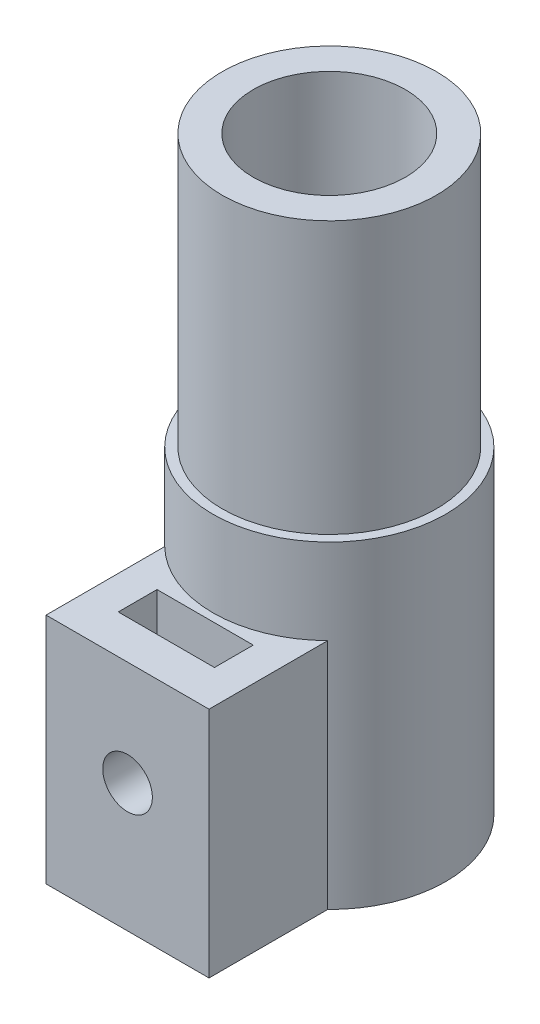
SolidWorks part; units mm, degrees
ref_plane "Front Plane" through (0, 0, 0) normal (0, 0, 1) x (1, 0, 0)
ref_plane "Top Plane" through (0, 0, 0) normal (0, 1, 0) x (1, 0, 0)
ref_plane "Right Plane" through (0, 0, 0) normal (1, 0, 0) x (0, 0, -1)
sketch "Sketch1" plane through (0, 0, 0) normal (0, 1, 0) x (1, 0, 0)
  circle A0 centre (0, 0) radius 6.9
  circle A1 centre (0, 0) radius 4.9
  dimension "D1" = 13.8
  dimension "D2" = 2
extrude "Boss-Extrude1" add sketch "Sketch1" against normal blind 38 contours A0
ref_plane "Plane1" through (0, -17.5, 0) normal (0, -1, 0) x (-1, 0, 0)
sketch "Sketch2" plane through (0, -17.5, 0) normal (0, -1, 0) x (-1, 0, 0)
  circle A0 centre (0, 0) radius 7.5
  circle A1 centre (0, 0) radius 6.9 construction
  circle A2 centre (0, 0) radius 6.9
  dimension "D1" = 15
extrude "Boss-Extrude2" add sketch "Sketch2" along normal through all contours A0
sketch "Sketch3" plane through (0, 0, 0) normal (0, 0, 1) x (1, 0, 0)
  line L0 (-5.25, -38) -> (-5.25, -23)
  line L1 (-7.5, -38) -> (7.5, -38) construction
  line L2 (-5.25, -23) -> (5.25, -23)
  line L3 (-5.25, -38) -> (5.25, -38)
  line L4 (5.25, -23) -> (5.25, -38)
  line L5 (5.25, -38) -> (-5.25, -38)
  point P4 (0, -23)
  dimension "D1" = 15
  dimension "D2" = 10.5
extrude "Boss-Extrude3" add sketch "Sketch3" against normal up to surface (7.6439 mm away) from offset 13 contours L4 L2 L0 L3
sketch "Sketch4" plane through (0, 0, 13) normal (0, 0, 1) x (1, 0, 0)
  line L0 (-3.1, -23) -> (-3.1, -29.75)
  line L1 (-5.25, -23) -> (5.25, -23) construction
  line L2 (-3.1, -23) -> (3.1, -23)
  line L3 (5.25, -23) -> (-5.25, -23) construction
  line L4 (3.1, -23) -> (3.1, -29.75)
  line L5 (-5.25, -38) -> (5.25, -38) construction
  arc A0 (-3.1, -29.75) -> (3.1, -29.75) centre (0, -29.75) ccw
  point P9 (0, -23)
  dimension "D2" = 8.25
  dimension "D1" = 6.2
extrude "Cut-Extrude1" cut sketch "Sketch4" against normal blind 2.5 from offset 2.5 offset against normal yes
sketch "Sketch5" plane through (0, 0, 13) normal (0, 0, 1) x (1, 0, 0)
  circle A0 centre (0, -29.75) radius 1.6
  dimension "D1" = 3.2
extrude "Cut-Extrude2" cut sketch "Sketch5" against normal blind 10
